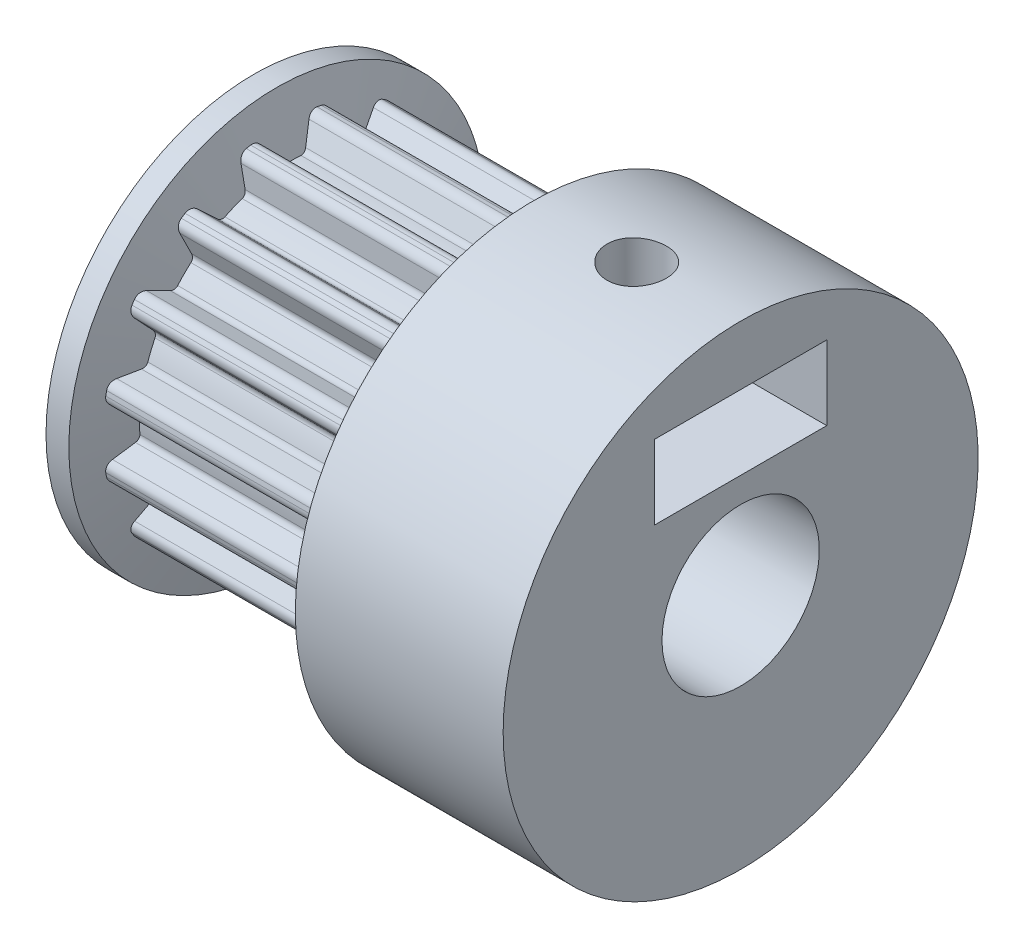
SolidWorks part; units mm, degrees
ref_plane "Front" through (0, 0, 0) normal (0, 0, 1) x (1, 0, 0)
ref_plane "Top" through (0, 0, 0) normal (0, 1, 0) x (1, 0, 0)
ref_plane "Right" through (0, 0, 0) normal (1, 0, 0) x (0, 0, -1)
sketch "Support-Cog" plane through (0, 0, 0) normal (1, 0, 0) x (0, 0, -1)
  line L0 (0, 0) -> (0, 6.1) construction
  line L3 (0.8861, 6.0353) -> (0.45, 5.1)
  line L4 (-0.8861, 6.0353) -> (-0.45, 5.1)
  line L5 (0.45, 5.1) -> (-0.45, 5.1) construction
  circle A1 centre (0, 0) radius 5.1198 construction
  circle A2 centre (0, 0) radius 6.1 construction
  arc A5 (0.7898, 5.8288) -> (1.1166, 5.9969) centre (1.0617, 5.702) cw
  arc A6 (-0.7898, 5.8288) -> (-1.1166, 5.9969) centre (-1.0617, 5.702) ccw
  circle A7 centre (0, 0) radius 2.65
  arc A8 (0.5084, 5.2252) -> (0.3148, 5.1101) centre (0.3271, 5.3097) cw
  arc A9 (-0.5084, 5.2252) -> (-0.3148, 5.1101) centre (-0.3271, 5.3097) ccw
  dimension "D1" = 50
  dimension "D2" = 0.9
  dimension "Diam-Gear" = 12.2
  dimension "Diam-Hole-Shaft" = 5.3
  dimension "D4" = 0.3
  dimension "D5" = 0.2
  dimension "D3" = 1
sketch "Support-Front" plane through (0, 0, 0) normal (0, 0, 1) x (1, 0, 0)
  line L0 (0, 0) -> (16, 0) construction
  line L1 (0, -2.65) -> (16, -2.65)
  line L2 (16, -8) -> (16, 8)
  line L3 (16, 8) -> (9, 8)
  line L4 (9, 8) -> (9, 6.1)
  line L5 (9, 6.1) -> (0, 6.1)
  line L6 (0, 6.1) -> (0, -6.1)
  line L7 (4.5, 6.1) -> (4.5, 0) construction
  line L8 (9, -6.1) -> (0, -6.1)
  line L9 (9, 8) -> (9, -8) construction
  line L10 (16, -8) -> (9, -8)
  line L11 (0, 6.1) -> (0, 8)
  line L12 (0, 2.65) -> (16, 2.65)
  line L13 (9, 6.1) -> (9, 8)
  line L14 (-0.3806, 7.8706) -> (0, 6.4501)
  line L15 (9, -8) -> (9, -6.1)
  line L16 (9, -6.1) -> (9, -8)
  line L17 (0, 6.4501) -> (0, 2.5423)
  line L18 (0.5, 2.5423) -> (0, 2.5423)
  line L19 (9, 2.5423) -> (9, 6.1)
  line L20 (0, -2.5423) -> (0, -6.1)
  line L21 (8.5, 6.5159) -> (8.5, 6.4501)
  line L22 (0, 2.5423) -> (0, 6.1)
  line L23 (9, -6.1) -> (9, -8)
  line L24 (9.3806, 7.8706) -> (8.8977, 8)
  line L25 (9, -8) -> (9, -6.1)
  line L26 (8.8977, 8) -> (8.5, 6.5159)
  line L27 (0.5, 2.5423) -> (0.5, 6.4501)
  line L28 (0.5, 6.4501) -> (0, 6.1) construction
  line L29 (9, 6.1) -> (9, 8)
  line L30 (0.5, 2.5423) -> (0, 6.1) construction
  line L31 (0, 6.4501) -> (0.5, 6.4501) construction
  line L34 (9, 6.4501) -> (8.5, 6.4501) construction
  line L35 (8.5, 2.5423) -> (8.5, 6.4501)
  line L36 (9, -2.5423) -> (9, -6.1)
  line L37 (9, 2.5423) -> (9, 6.1)
  line L38 (8.5, 2.5423) -> (9, 2.5423)
  line L39 (0.1023, 8) -> (0.5, 6.5159)
  line L40 (9, 6.4501) -> (9, 2.5423)
  line L41 (-0.3806, 7.8706) -> (0.1023, 8)
  line L42 (9.3806, 7.8706) -> (9, 6.4501)
  line L43 (9, 6.1) -> (9, 8)
  line L44 (0.5, -6.5159) -> (0.5, -6.4501)
  line L45 (9, -6.1) -> (9, -8)
  line L46 (9.3806, -7.8706) -> (9, -6.4501)
  line L47 (-0.3806, -7.8706) -> (0.1023, -8)
  line L48 (9, -6.4501) -> (9, -2.5423)
  line L49 (0.5, 6.5159) -> (0.5, 6.4501)
  line L50 (0.1023, -8) -> (0.5, -6.5159)
  line L51 (8.5, -2.5423) -> (9, -2.5423)
  line L52 (9, -2.5423) -> (9, -6.1)
  line L53 (8.5, -2.5423) -> (8.5, -6.4501)
  line L54 (9, -6.4501) -> (8.5, -6.4501) construction
  line L55 (0, -6.4501) -> (0.5, -6.4501) construction
  line L56 (9, -6.1) -> (9, -8)
  line L57 (0.5, -2.5423) -> (0.5, -6.4501)
  line L58 (8.8977, -8) -> (8.5, -6.5159)
  line L59 (9.3806, -7.8706) -> (8.8977, -8)
  line L60 (0, -2.5423) -> (0, -6.1)
  line L61 (8.5, -6.5159) -> (8.5, -6.4501)
  line L62 (9, -2.5423) -> (9, -6.1)
  line L63 (0.5, -2.5423) -> (0, -2.5423)
  line L64 (0, -6.4501) -> (0, -2.5423)
  line L65 (-0.3806, -7.8706) -> (0, -6.4501)
  line L66 (9, -6.1) -> (9, -8)
  line L67 (0, -6.1) -> (0, -8)
  line L68 (9, -6.1) -> (0, -6.1)
  line L69 (9, -8) -> (9, -6.1)
  line L70 (0, 6.4501) -> (0.5, 6.5159) construction
  dimension "D1" = 55
  dimension "Diam-Hub" = 16
  dimension "D2" = 8
  dimension "D3" = 15
  dimension "Width-Total" = 16
  dimension "Width-Cog" = 9
  dimension "Thickn-Flange" = 0.5
  dimension "Diam-Flange" = 16
sketch "Support-Key" plane through (0, 0, 0) normal (1, 0, 0) x (0, 0, -1)
  line L0 (0, -2.65) -> (0, 197.35) construction
  line L1 (0, 0) -> (0, 6.1) construction
  line L2 (1, 197.35) -> (-1, 197.35)
  line L3 (-1, 197.35) -> (-1, 0)
  line L4 (1, 197.35) -> (1, 0)
  line L5 (-1, 0) -> (1, 0)
  circle A0 centre (0, 0) radius 2.65 construction
  point P12 (0, 0)
  dimension "Height-Key" = 200
  dimension "Width-Key" = 2
sketch "Support-Stop-Screw" plane through (0, 0, 0) normal (0, 0, 1) x (1, 0, 0)
  line L0 (12.5, 0) -> (12.5, 197.35) construction
  line L1 (0, 0) -> (16, 0) construction
  line L2 (0, 0) -> (0, 6.1) construction
  line L3 (13.5, 197.35) -> (0, 197.35) construction
  line L4 (11.5, 197.35) -> (13.5, 197.35)
  line L5 (13.5, 197.35) -> (13.5, 0)
  line L6 (11.5, 197.35) -> (11.5, 0)
  line L7 (13.5, 0) -> (11.5, 0)
  line L8 (0, -2.65) -> (0, 197.35) construction
  dimension "Dist-Hole-Stop-Screw" = 12.5
  dimension "Diam-Stop-Screw" = 2
sketch "Sketch2" plane through (0, 0, 0) normal (0, 0, 1) x (1, 0, 0)
  line L5 (0, 0) -> (16, 0) construction
  line L10 (9, 6.1) -> (0, 6.1) construction
  line L11 (0, 0) -> (0, 6.1) construction
  line L12 (0, 0) -> (9, 0)
  line L13 (9, 0) -> (9, 6.1)
  line L15 (9, 6.1) -> (0, 6.1)
  line L16 (0, 0) -> (0, 6.1)
  line L17 (0, 0) -> (16, 0) construction
revolve "Body" add sketch "Sketch2" angle 360 about L17
sketch "Sketch6" plane through (0, 0, 0) normal (1, 0, 0) x (0, 0, -1)
  line L0 (0.8861, 6.0353) -> (0.45, 5.1) construction
  line L1 (-0.8861, 6.0353) -> (-0.45, 5.1) construction
  line L2 (0.7898, 5.8288) -> (0.5084, 5.2252)
  line L3 (-0.7898, 5.8288) -> (-0.5084, 5.2252)
  arc A0 (0.3148, 5.1101) -> (0.5084, 5.2252) centre (0.3271, 5.3097) ccw construction
  circle A1 centre (0, 0) radius 5.1198 construction
  arc A2 (-0.5084, 5.2252) -> (-0.3148, 5.1101) centre (-0.3271, 5.3097) ccw construction
  arc A3 (-0.7898, 5.8288) -> (-1.1166, 5.9969) centre (-1.0617, 5.702) ccw construction
  circle A4 centre (0, 0) radius 6.1 construction
  arc A5 (1.1166, 5.9969) -> (0.7898, 5.8288) centre (1.0617, 5.702) ccw construction
  arc A6 (0.3148, 5.1101) -> (0.5084, 5.2252) centre (0.3271, 5.3097) ccw
  arc A7 (0.3148, 5.1101) -> (-0.3148, 5.1101) centre (0, 0) ccw
  arc A8 (-0.5084, 5.2252) -> (-0.3148, 5.1101) centre (-0.3271, 5.3097) ccw
  arc A9 (-0.7898, 5.8288) -> (-1.1166, 5.9969) centre (-1.0617, 5.702) ccw
  arc A10 (1.1166, 5.9969) -> (-1.1166, 5.9969) centre (0, 0) ccw
  arc A11 (1.1166, 5.9969) -> (0.7898, 5.8288) centre (1.0617, 5.702) ccw
extrude "Cog" cut sketch "Sketch6" along normal through all
pattern_circular "Pattern-Cog" count 16 over 360 about axis through (0, 0, 0) along (1, 0, 0) of "Cog"
sketch "Sketch3" plane through (0, 0, 0) normal (0, 0, 1) x (1, 0, 0)
  line L2 (16, 8) -> (9, 8) construction
  line L3 (16, -8) -> (16, 8) construction
  line L4 (9, 0) -> (16, 0)
  line L5 (16, 8) -> (9, 8)
  line L6 (9, 8) -> (9, 0)
  line L7 (0, 0) -> (16, 0) construction
  line L8 (0, 0) -> (16, 0) construction
  line L10 (16, 0) -> (16, 8)
revolve "Hub" add sketch "Sketch3" angle 360 about L8
sketch "Sketch8" plane through (0, 0, 0) normal (0, 0, 1) x (1, 0, 0)
  line L0 (16, -8) -> (16, 8) construction
  line L1 (0, 6.1) -> (0, -6.1) construction
  line L2 (0, -2.65) -> (16, -2.65) construction
  line L3 (16, 0) -> (16, -2.65)
  line L4 (0, -2.65) -> (0, 0)
  line L5 (0, -2.65) -> (16, -2.65)
  line L6 (0, 0) -> (16, 0) construction
  line L7 (0, 0) -> (16, 0) construction
  line L8 (0, 0) -> (16, 0)
revolve "Hole-Shaft" cut sketch "Sketch8" angle 360 about L7
sketch "Sketch11" plane through (0, 0, 0) normal (1, 0, 0) x (0, 0, -1)
  line L4 (1, 197.35) -> (-1, 197.35)
  line L5 (-1, 197.35) -> (-1, 0)
  line L6 (-1, 0) -> (1, 0)
  line L7 (1, 0) -> (1, 197.35)
  line L8 (1, 197.35) -> (-1, 197.35)
  line L9 (-1, 197.35) -> (-1, 0)
  line L10 (-1, 0) -> (1, 0)
  line L11 (1, 0) -> (1, 197.35)
  dimension "D1" = 0
extrude "Key" [suppressed] cut sketch "Sketch11" along normal through all
sketch "Sketch15" plane through (0, 0, 0) normal (0, 0, 1) x (1, 0, 0)
  line L0 (12.5, 197.35) -> (12.5, 0) construction
  line L1 (12.5, 197.35) -> (13.5, 197.35)
  line L2 (13.5, 197.35) -> (13.5, 0)
  line L3 (13.5, 0) -> (12.5, 0)
  line L4 (12.5, 197.35) -> (12.5, 0)
revolve "Stop-Screw" cut sketch "Sketch15" angle 360 about L0
pattern_circular "Pattern-Stop-Screw" [suppressed] count 2 every 90 about axis through (0, 0, 0) along (1, 0, 0)
sketch "Sketch16" plane through (0, 0, 0) normal (0, 0, 1) x (1, 0, 0)
  line L0 (0, 2.5423) -> (-0.3981, 2.5423)
  line L1 (0.5, 2.5423) -> (0, 2.5423) construction
  line L2 (-0.3981, 2.5423) -> (-0.3981, 7)
  line L3 (0.3703, 7) -> (-0.3981, 7)
  line L4 (1.1019, 4.2696) -> (1.1019, 2.5423)
  line L7 (0.1023, 8) -> (0.5, 6.5159) construction
  line L11 (1.1019, 2.5423) -> (0, 2.5423)
  line L12 (0, 0) -> (16, 0) construction
  line L13 (0, 0) -> (16, 0) construction
  line L16 (0.3703, 7) -> (1.1019, 4.2696)
  dimension "D1" = 1.5
  dimension "D2" = 7
revolve "Flange-Left" add sketch "Sketch16" angle 360 about L13
sketch "Sketch17" plane through (0, 0, 0) normal (0, 0, 1) x (1, 0, 0)
  line L0 (0, 0) -> (16, 0) construction
  line L1 (9, 6.4501) -> (9, 2.5423) construction
  line L2 (9.3806, 7.8706) -> (8.8977, 8) construction
  line L3 (8.8977, 8) -> (8.5, 6.5159) construction
  line L5 (0, 0) -> (9, 0) construction
  line L9 (8.5, 6.5159) -> (8.5, 6.4501) construction
  line L10 (8.5, 2.5423) -> (8.5, 6.4501) construction
  line L11 (8.5, 2.5423) -> (9, 2.5423) construction
  line L12 (9.3806, 7.8706) -> (9, 6.4501) construction
  line L13 (9, 6.4501) -> (9, 2.5423)
  line L14 (9.3806, 7.8706) -> (8.8977, 8)
  line L15 (8.8977, 8) -> (8.5, 6.5159)
  line L16 (8.5, 6.5159) -> (8.5, 6.4501)
  line L17 (8.5, 2.5423) -> (8.5, 6.4501)
  line L18 (8.5, 2.5423) -> (9, 2.5423)
  line L19 (9.3806, 7.8706) -> (9, 6.4501)
revolve "Flange-Right" [suppressed] add sketch "Sketch17" angle 360 about L5
ref_plane "Plane1" through (0, 3.5, 0) normal (0, 1, 0) x (-1, 0, 0)
sketch "Sketch18" plane through (0, 3.5, 0) normal (0, 1, 0) x (-1, 0, 0)
  line L0 (-16.4174, 2.9) -> (-16.4174, -2.9)
  line L1 (-9.1514, 0) -> (-10.8257, 2.9)
  line L2 (-10.8257, 2.9) -> (-16.4174, 2.9)
  line L5 (-16.4174, -2.9) -> (-10.8257, -2.9)
  line L6 (-10.8257, -2.9) -> (-9.1514, 0)
  line L8 (-15.0115, 1.45) -> (-15.8692, -0.0357) [skipped]
  line L9 (-15.0115, -1.45) -> (-14.1537, -2.9357) [skipped]
  circle A0 centre (-12.5, 0) radius 2.9 construction
  circle A1 centre (-12.5, 0) radius 1 construction
  dimension "D1" = 5.8
extrude "Cut-Extrude1" cut sketch "Sketch18" along normal blind 2.5
equation "\"Dist-Hole-Stop-Screw@Support-Stop-Screw\"=\"Width-Cog@Support-Front\"+(\"Width-Total@Support-Front\"-\"Width-Cog@Support-Front\")/2"
